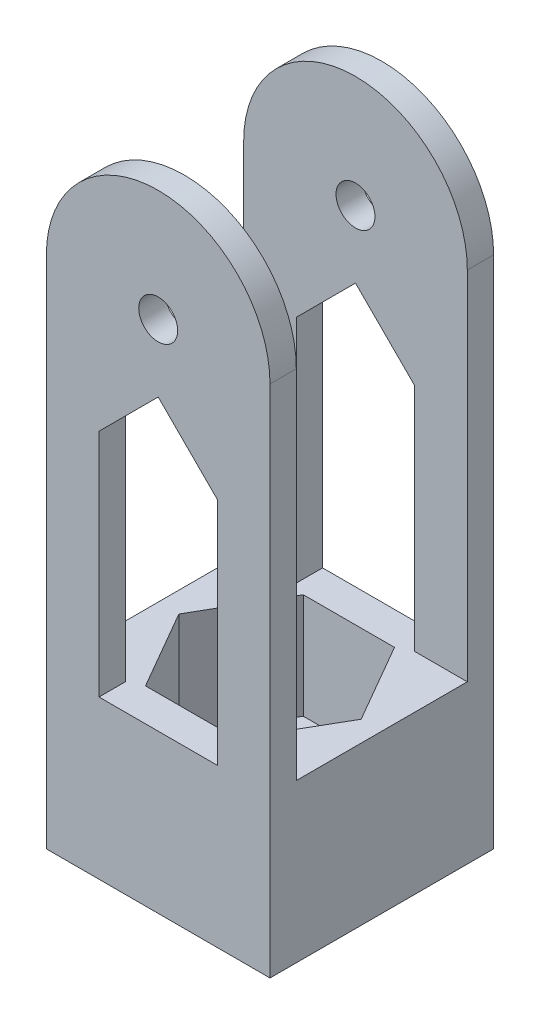
SolidWorks part; units mm, degrees
ref_plane "Front Plane" through (0, 0, 0) normal (0, 0, 1) x (1, 0, 0)
ref_plane "Top Plane" through (0, 0, 0) normal (0, 1, 0) x (1, 0, 0)
ref_plane "Right Plane" through (0, 0, 0) normal (1, 0, 0) x (0, 0, -1)
sketch "Sketch1" plane through (0, 0, 0) normal (0, 1, 0) x (1, 0, 0)
  line L1 (0, 0) -> (26.9875, 0)
  line L2 (0, 0) -> (0, 26.9875)
  line L3 (0, 26.9875) -> (26.9875, 26.9875)
  line L4 (26.9875, 0) -> (26.9875, 26.9875)
  dimension "D1" = 26.9875
extrude "Boss-Extrude1" add sketch "Sketch1" along normal blind 19.05 contours L2 L3 L4 L1
sketch "Sketch2" plane through (0, 19.05, 0) normal (0, 1, 0) x (1, 0, 0)
  line L0 (0, 0) -> (0, 26.9875) construction
  line L1 (0, 26.9875) -> (26.9875, 26.9875) construction
  circle A0 centre (13.4937, 13.4937) radius 6.985
  point P4 (0, 13.4937)
  point P7 (13.4937, 26.9875)
  dimension "D1" = 13.97
extrude "Cut-Extrude1" cut sketch "Sketch2" against normal through all
sketch "Sketch3" plane through (0, 19.05, 0) normal (0, 1, 0) x (1, 0, 0)
  line L0 (0, 26.9875) -> (26.9875, 26.9875) construction
  line L1 (18.993, 23.0188) -> (7.9945, 23.0188)
  line L2 (7.9945, 23.0188) -> (2.4952, 13.4938)
  line L3 (2.4952, 13.4938) -> (7.9945, 3.9687)
  line L4 (7.9945, 3.9687) -> (18.993, 3.9687)
  line L5 (18.993, 3.9687) -> (24.4923, 13.4937)
  line L6 (24.4923, 13.4937) -> (18.993, 23.0188)
  circle A0 centre (13.4937, 13.4937) radius 9.525 construction
  dimension "D1" = 19.05
extrude "Cut-Extrude4" cut sketch "Sketch3" against normal blind 12.7 contours L2 L3 L4 L5 L6 L1
sketch "Sketch4" plane through (0, 0, -26.9875) normal (0, 0, -1) x (-1, 0, 0)
  line L0 (0, 19.05) -> (-26.9875, 19.05)
  line L1 (-26.9875, 19.05) -> (-26.9875, 62.0875)
  line L3 (0, 62.0875) -> (0, 19.05)
  line L4 (0, 48.5937) -> (-26.9875, 48.5937) construction
  circle A0 centre (-13.4937, 62.0875) radius 2.3495
  arc A1 (0, 62.0875) -> (-26.9875, 62.0875) centre (-13.4937, 62.0875) ccw
  circle A2 centre (-49.6792, 35) radius 13.5937 construction
  dimension "D1" = 4.699
extrude "Boss-Extrude2" add sketch "Sketch4" against normal blind 3.175
ref_plane "Plane2" through (0, 0, -13.4937) normal (0, 0, -1) x (-1, 0, 0)
mirror "Mirror1" about plane through (0, 0, -13.4937) normal (0, 0, -1) of "Boss-Extrude2"
sketch "Sketch6" plane through (0, 0, -26.9875) normal (0, 0, -1) x (-1, 0, 0)
  line L0 (-20.6375, 46.8313) -> (-13.4938, 53.975)
  line L1 (-20.6375, 19.05) -> (-6.35, 19.05)
  line L2 (-20.6375, 19.05) -> (-20.6375, 46.8313)
  line L3 (-13.4938, 19.05) -> (-13.4937, 0) construction
  line L4 (-6.35, 19.05) -> (-6.35, 46.8312)
  line L5 (-13.4938, 53.975) -> (-6.35, 46.8312)
  line L6 (0, 0) -> (-26.9875, 0) construction
  line L7 (-26.9875, 19.05) -> (0, 19.05) construction
  line L8 (0, 62.0875) -> (0, 0) construction
  dimension "D3" = 34.925
  dimension "D1" = 135
  dimension "D2" = 6.35
extrude "Cut-Extrude5" cut sketch "Sketch6" against normal through all
